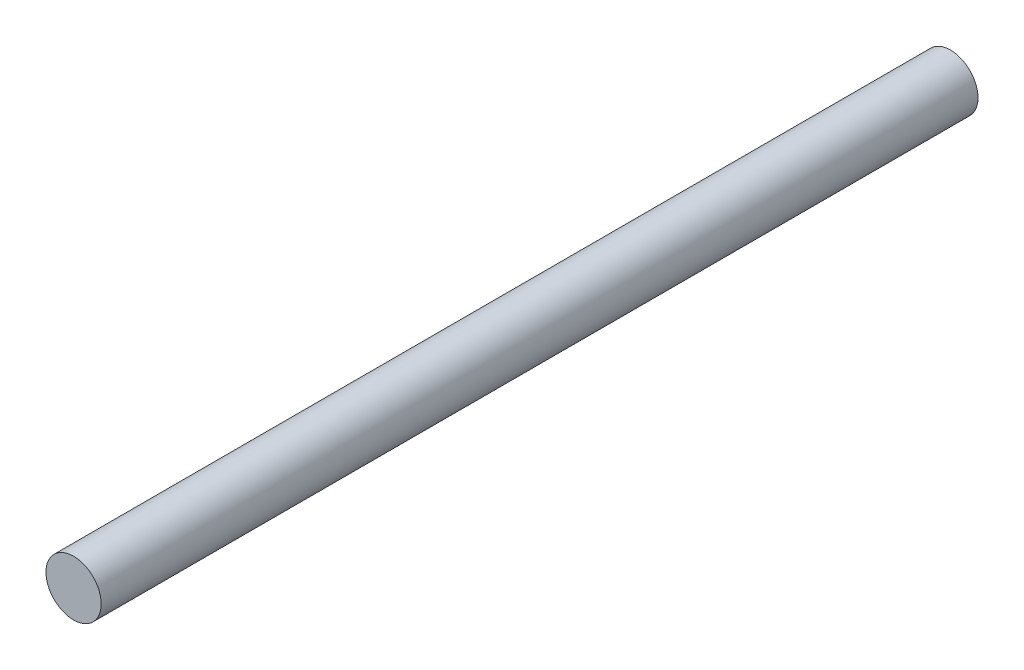
SolidWorks part; units mm, degrees
ref_plane "Front Plane" through (0, 0, 0) normal (0, 0, 1) x (1, 0, 0)
ref_plane "Top Plane" through (0, 0, 0) normal (0, 1, 0) x (1, 0, 0)
ref_plane "Right Plane" through (0, 0, 0) normal (1, 0, 0) x (0, 0, -1)
sketch "Sketch1" plane through (0, 0, 0) normal (0, 0, 1) x (1, 0, 0)
  circle A0 centre (0, 0) radius 4
  dimension "D1" = 8
extrude "Boss-Extrude1" add sketch "Sketch1" along normal blind 127
